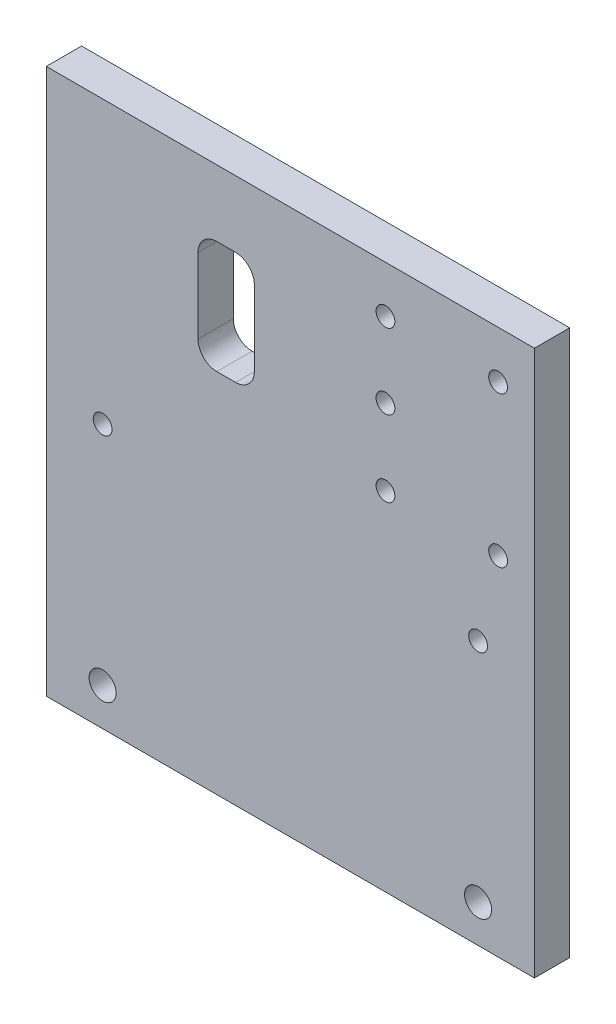
SolidWorks part; units mm, degrees
ref_plane "Front Plane" through (0, 0, 0) normal (0, 0, 1) x (1, 0, 0)
ref_plane "Top Plane" through (0, 0, 0) normal (0, 1, 0) x (1, 0, 0)
ref_plane "Right Plane" through (0, 0, 0) normal (1, 0, 0) x (0, 0, -1)
sketch "Sketch1" plane through (0, 0, 0) normal (0, 0, 1) x (1, 0, 0)
  line L0 (75.33, 84.625) -> (75.33, 80.485) construction
  line L5 (0, 0) -> (100, 0) construction
  line L6 (0, 0) -> (0, 60.26) construction
  line L7 (0, 60.26) -> (100, 60.26) construction
  line L8 (100, 0) -> (100, 60.26) construction
  line L9 (0, 0) -> (100, 60.26) construction
  line L10 (0, 60.26) -> (100, 0) construction
  line L11 (-15, -10) -> (115, -10)
  line L12 (-15, -10) -> (-15, 135.26)
  line L13 (-15, 135.26) -> (115, 135.26)
  line L14 (115, -10) -> (115, 135.26)
  line L15 (-15, -10) -> (115, 135.26) construction
  line L16 (-15, 135.26) -> (115, -10) construction
  line L17 (58.97, 84.625) -> (109.14, 84.625) construction
  line L18 (109.14, 80.485) -> (58.97, 80.485) construction
  line L19 (105.33, 124.705) -> (105.33, 120.565) construction
  line L20 (58.97, 124.705) -> (109.14, 124.705) construction
  line L21 (109.14, 120.565) -> (58.97, 120.565) construction
  line L22 (105.33, 84.625) -> (105.33, 80.485) construction
  line L23 (75.33, 122.7664) -> (75.33, 84.625) construction
  circle A0 centre (0, 0) radius 3.6
  circle A1 centre (0, 60.26) radius 2.5
  circle A2 centre (100, 60.26) radius 2.5
  circle A3 centre (100, 0) radius 3.6
  circle A4 centre (75.33, 82.555) radius 2.5
  circle A5 centre (105.33, 82.555) radius 2.5
  circle A6 centre (105.33, 122.635) radius 2.5
  circle A8 centre (75.33, 102.7664) radius 2.5
  circle A9 centre (75.33, 122.7664) radius 2.5
  point P6 (50, 30.13)
  point P16 (50, 62.63)
  dimension "D1" = 7.2
  dimension "D3" = 5
  dimension "D9" = 30
  dimension "D10" = 5
  dimension "D11" = 5
  dimension "D12" = 5
  dimension "D13" = 5
  dimension "D2" = 60.26
  dimension "D4" = 100
  dimension "D5" = 15
  dimension "D6" = 15
  dimension "D7" = 10
  dimension "D8" = 75
extrude "Boss-Extrude1" add sketch "Sketch1" along normal blind 9.4
sketch "Sketch2" plane through (0, 0, 0) normal (0, 0, -1) x (-1, 0, 0)
  line L0 (-115, 135.26) -> (15, 135.26) construction
  line L1 (-40.4075, 87.5704) -> (-25.4075, 87.5704)
  line L2 (-40.4075, 87.5704) -> (-40.4075, 117.5704)
  line L3 (-40.4075, 117.5704) -> (-25.4075, 117.5704)
  line L4 (-25.4075, 87.5704) -> (-25.4075, 117.5704)
  line L5 (-40.4075, 87.5704) -> (-25.4075, 117.5704) construction
  line L6 (-40.4075, 117.5704) -> (-25.4075, 87.5704) construction
  point P4 (-32.9075, 102.5704)
  dimension "D1" = 30
  dimension "D2" = 15
  dimension "D3" = 17.6896
extrude "Cut-Extrude1" cut sketch "Sketch2" against normal through all
fillet "Fillet1" radius 5 4 edges at (25.4075, 117.5704, 4.7) (40.4075, 117.5704, 4.7) (25.4075, 87.5704, 4.7) (40.4075, 87.5704, 4.7)
